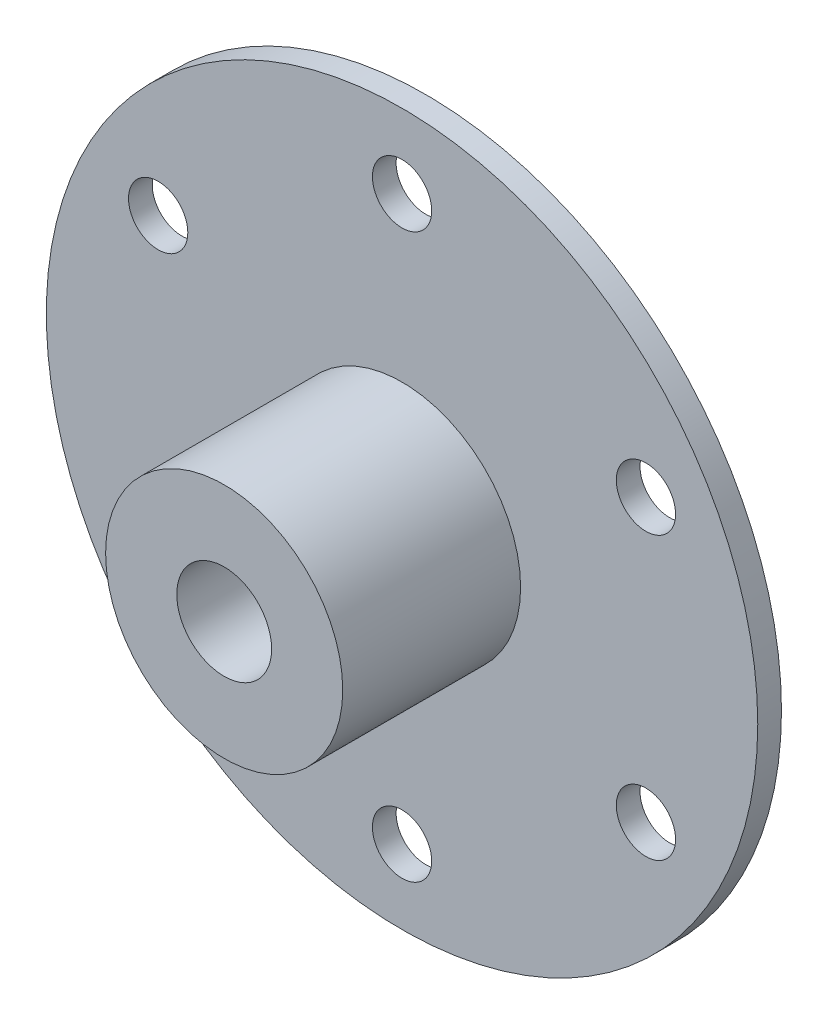
SolidWorks part; units mm, degrees
ref_plane "Front Plane" through (0, 0, 0) normal (0, 0, 1) x (1, 0, 0)
ref_plane "Top Plane" through (0, 0, 0) normal (0, 1, 0) x (1, 0, 0)
ref_plane "Right Plane" through (0, 0, 0) normal (1, 0, 0) x (0, 0, -1)
sketch "Sketch1" plane through (0, 0, 0) normal (0, 0, 1) x (1, 0, 0)
  circle A0 centre (0, 0) radius 30
  circle A2 centre (0, 23.75) radius 2.5
  circle A3 centre (20.5681, 11.875) radius 2.5
  circle A4 centre (20.5681, -11.875) radius 2.5
  circle A5 centre (0, -23.75) radius 2.5
  circle A6 centre (-20.5681, -11.875) radius 2.5
  circle A7 centre (-20.5681, 11.875) radius 2.5
  point P19 (0, 0)
  dimension "D1" = 60
  dimension "D3" = 5
  dimension "D4" = 6
extrude "Boss-Extrude1" add sketch "Sketch1" along normal blind 2
sketch "Sketch2" plane through (0, 0, 2) normal (0, 0, 1) x (1, 0, 0)
  circle A0 centre (0, 0) radius 4
  circle A1 centre (0, 0) radius 10
  dimension "D1" = 8
  dimension "D2" = 20
extrude "Boss-Extrude2" add sketch "Sketch2" along normal blind 15
